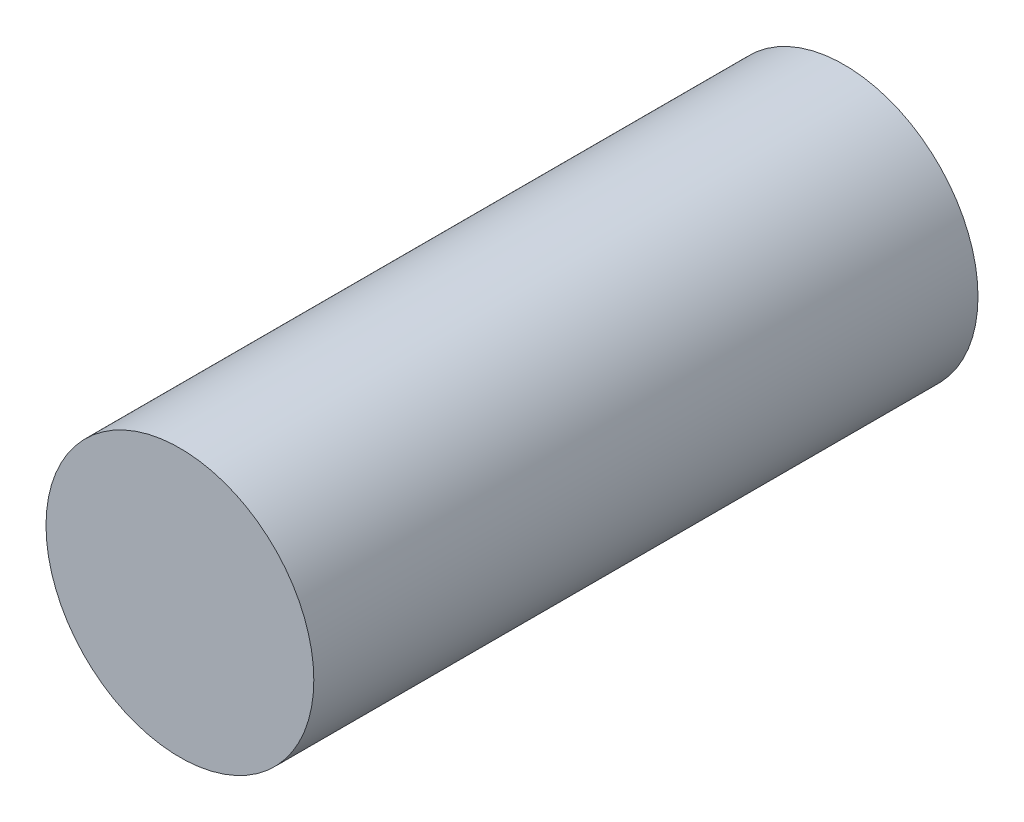
SolidWorks part; units mm, degrees
material "AISI 1020"
ref_plane "Спереди" through (0, 0, 0) normal (0, 0, 1) x (1, 0, 0)
ref_plane "Сверху" through (0, 0, 0) normal (0, 1, 0) x (1, 0, 0)
ref_plane "Справа" through (0, 0, 0) normal (1, 0, 0) x (0, 0, -1)
sketch "Эскиз1" plane through (0, 0, 0) normal (0, 0, 1) x (1, 0, 0)
  circle A0 centre (0, 0) radius 2.5
  dimension "D1" = 5
extrude "Бобышка-Вытянуть1" add sketch "Эскиз1" against normal up to surface (12.4 mm away) from offset 0.5 contours A0
